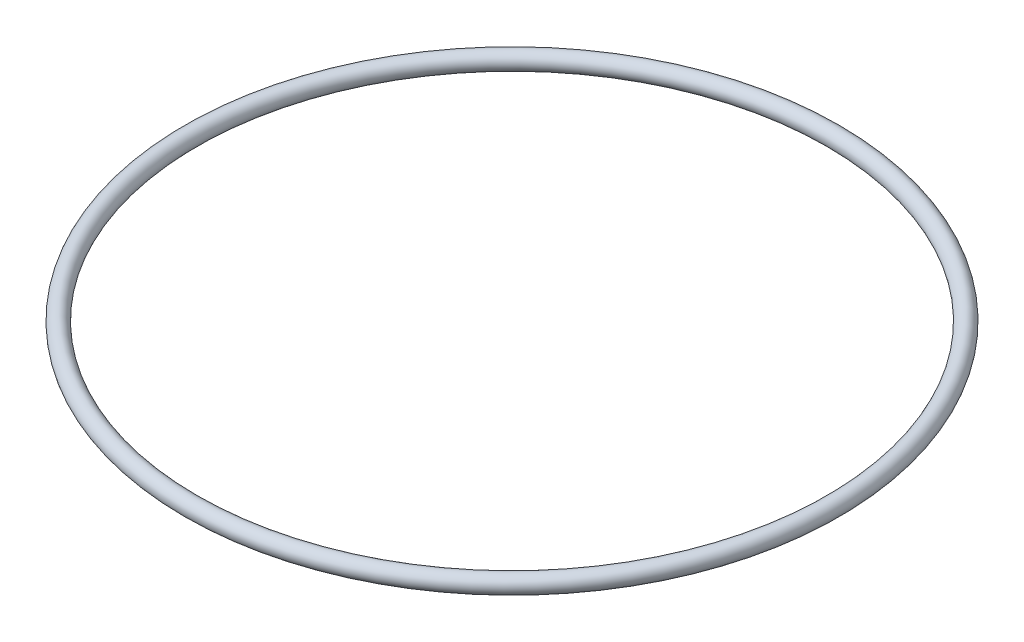
SolidWorks part; units mm, degrees
material "BUTYL"
ref_plane "Front Plane" through (0, 0, 0) normal (0, 0, 1) x (1, 0, 0)
ref_plane "Top Plane" through (0, 0, 0) normal (0, 1, 0) x (1, 0, 0)
ref_plane "Right Plane" through (0, 0, 0) normal (1, 0, 0) x (0, 0, -1)
sketch "Sketch1" plane through (0, 0, 0) normal (0, 0, 1) x (1, 0, 0)
  circle A0 centre (29.3687, 0) radius 0.7937
  dimension "D2" = 1.5875
  dimension "D1" = 29.3687
ref_axis "Axis1" through (0, 6.6674, 0) along (0, -1, 0)
revolve "Revolve2" add sketch "Sketch1" angle 360 about axis through (0, 6.6674, 0) along (0, -1, 0)
